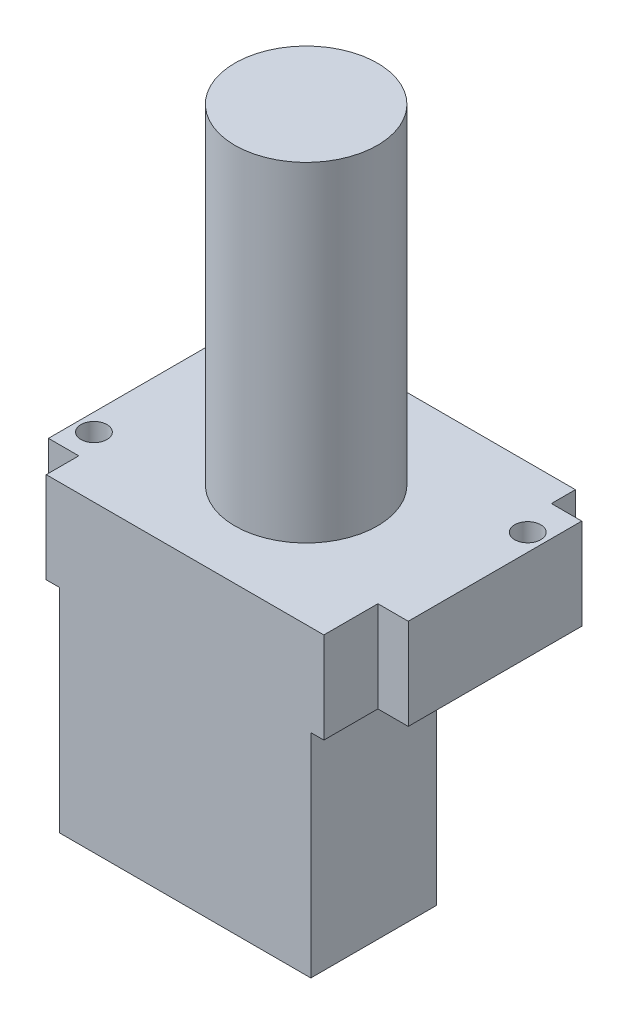
SolidWorks part; units mm, degrees
ref_plane "前基準面" through (0, 0, 0) normal (0, 0, 1) x (1, 0, 0)
ref_plane "上基準面" through (0, 0, 0) normal (0, 1, 0) x (1, 0, 0)
ref_plane "右基準面" through (0, 0, 0) normal (1, 0, 0) x (0, 0, -1)
sketch "草圖1" plane through (0, 0, 0) normal (0, 1, 0) x (1, 0, 0)
  line L1 (-14.5, 7.25) -> (14.5, 7.25)
  line L2 (-14.5, 7.25) -> (-14.5, -7.25)
  line L3 (-14.5, -7.25) -> (14.5, -7.25)
  line L4 (14.5, 7.25) -> (14.5, -7.25)
  line L5 (-14.5, 7.25) -> (14.5, -7.25) construction
  line L6 (-14.5, -7.25) -> (14.5, 7.25) construction
  point P0 (0, 0)
extrude "填料-伸長1" add sketch "草圖1" along normal blind 24.5
sketch "草圖3" plane through (0, 24.5, 0) normal (0, 1, 0) x (1, 0, 0)
  line L0 (-14.5, -7.25) -> (14.5, -7.25) construction
  line L1 (-16, 21.75) -> (16, 21.75)
  line L2 (-16, 21.75) -> (-16, -7.25)
  line L3 (-16, -7.25) -> (16, -7.25)
  line L4 (16, 21.75) -> (16, -7.25)
  line L5 (-16, 21.75) -> (16, -7.25) construction
  line L6 (-16, -7.25) -> (16, 21.75) construction
  line L7 (14.5, 7.25) -> (-14.5, 7.25) construction
  point P1 (0, 7.25)
  point P8 (0, 7.25)
  dimension "D1" = 0
  dimension "D2" = 32
  dimension "D3" = 29
extrude "填料-伸長3" add sketch "草圖3" along normal blind 10.5
sketch "草圖6" plane through (16, 0, 0) normal (1, 0, 0) x (0, 0, -1)
  line L0 (-7.25, 35) -> (21.75, 35) construction
  line L1 (18.9789, 35) -> (-1.0211, 35)
  line L2 (18.9789, 35) -> (18.9789, 24.5)
  line L3 (18.9789, 24.5) -> (-1.0211, 24.5)
  line L4 (-1.0211, 35) -> (-1.0211, 24.5)
  line L5 (-7.25, 24.5) -> (21.75, 24.5) construction
extrude "填料-伸長5" add sketch "草圖6" along normal blind 3.5
sketch "草圖8" plane through (-16, 0, 0) normal (-1, 0, 0) x (0, 0, 1)
  line L0 (-21.75, 24.5) -> (7.25, 24.5) construction
  line L1 (-16.5031, 24.5) -> (3.4969, 24.5)
  line L2 (-16.5031, 24.5) -> (-16.5031, 35)
  line L3 (-16.5031, 35) -> (3.4969, 35)
  line L4 (3.4969, 24.5) -> (3.4969, 35)
  line L5 (-21.75, 35) -> (7.25, 35) construction
extrude "填料-伸長6" add sketch "草圖8" along normal blind 3.5
sketch "草圖9" plane through (0, 35, 0) normal (0, 1, 0) x (1, 0, 0)
  line L0 (16, 21.75) -> (-16, 21.75) construction
  line L1 (-16, -7.25) -> (16, -7.25) construction
  line L2 (-19.5, -3.4969) -> (-19.5, 16.5031) construction
  line L3 (19.5, 18.9789) -> (19.5, -1.0211) construction
  circle A0 centre (17.5, 14.75) radius 1.5
  circle A1 centre (-17.5, -0.25) radius 1.5
  dimension "D1" = 7
  dimension "D2" = 7
  dimension "D3" = 2
  dimension "D4" = 2
extrude "除料-伸長1" cut sketch "草圖9" against normal through all
sketch "草圖11" plane through (0, 35, 0) normal (0, 1, 0) x (1, 0, 0)
  circle A0 centre (0, 6.7095) radius 8.2171
extrude "填料-伸長7" add sketch "草圖11" along normal blind 38
